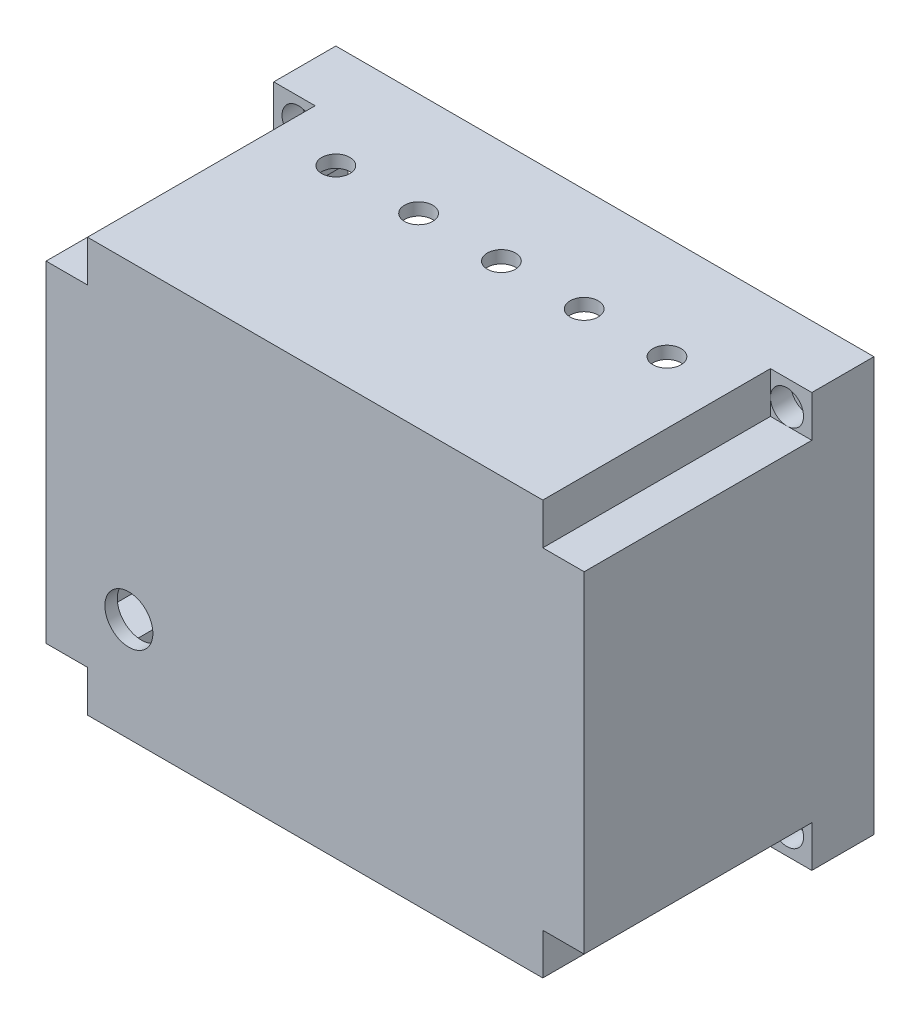
SolidWorks part; units mm, degrees
ref_plane "Front Plane" through (0, 0, 0) normal (0, 0, 1) x (1, 0, 0)
ref_plane "Top Plane" through (0, 0, 0) normal (0, 1, 0) x (1, 0, 0)
ref_plane "Right Plane" through (0, 0, 0) normal (1, 0, 0) x (0, 0, -1)
sketch "Sketch2" plane through (0, 0, 0) normal (0, 1, 0) x (1, 0, 0)
  line L1 (0, 0) -> (130, 0)
  line L2 (0, 0) -> (0, 70)
  line L3 (0, 70) -> (130, 70)
  line L4 (130, 0) -> (130, 70)
  dimension "D1" = 130
  dimension "D2" = 70
extrude "Boss-Extrude1" add sketch "Sketch2" along normal blind 100
sketch "Sketch3" plane through (0, 0, -70) normal (0, 0, -1) x (-1, 0, 0)
  line L0 (-130, 100) -> (0, 100) construction
  line L1 (-117, 87) -> (-13, 87)
  line L2 (-117, 87) -> (-117, 13)
  line L3 (-117, 13) -> (-13, 13)
  line L4 (-13, 87) -> (-13, 13)
  line L5 (-117, 87) -> (-13, 13) construction
  line L6 (-117, 13) -> (-13, 87) construction
  line L7 (-130, 100) -> (-130, 0) construction
  line L8 (-130, 0) -> (0, 0) construction
  line L9 (0, 100) -> (0, 0) construction
  point P0 (-65, 50)
  dimension "D1" = 13
  dimension "D2" = 13
  dimension "D3" = 13
  dimension "D4" = 13
extrude "Cut-Extrude1" cut sketch "Sketch3" against normal blind 67
sketch "Sketch4" plane through (0, 0, 0) normal (0, 0, 1) x (1, 0, 0)
  line L1 (0, 100) -> (10, 100)
  line L2 (0, 100) -> (0, 90)
  line L3 (0, 90) -> (10, 90)
  line L4 (10, 100) -> (10, 90)
  line L5 (130, 100) -> (120, 100)
  line L6 (130, 100) -> (130, 90)
  line L7 (130, 90) -> (120, 90)
  line L8 (120, 100) -> (120, 90)
  line L9 (0, 0) -> (10, 0)
  line L10 (0, 0) -> (0, 10)
  line L11 (0, 10) -> (10, 10)
  line L12 (10, 0) -> (10, 10)
  line L13 (130, 0) -> (120, 0)
  line L14 (130, 0) -> (130, 10)
  line L15 (130, 10) -> (120, 10)
  line L16 (120, 0) -> (120, 10)
  dimension "D1" = 10
  dimension "D2" = 10
  dimension "D3" = 10
  dimension "D4" = 10
  dimension "D5" = 10
  dimension "D6" = 10
  dimension "D7" = 10
  dimension "D8" = 10
extrude "Cut-Extrude2" cut sketch "Sketch4" against normal blind 55
sketch "Sketch5" plane through (0, 0, -70) normal (0, 0, -1) x (-1, 0, 0)
  line L0 (-130, 100) -> (0, 100) construction
  line L1 (-117, 87) -> (-13, 87)
  line L2 (-117, 87) -> (-117, 97)
  line L3 (-117, 97) -> (-13, 97)
  line L4 (-13, 87) -> (-13, 97)
  line L9 (-13, 13) -> (-117, 13)
  line L10 (-13, 13) -> (-13, 3)
  line L11 (-13, 3) -> (-117, 3)
  line L12 (-117, 13) -> (-117, 3)
  line L18 (-130, 0) -> (0, 0) construction
  dimension "D1" = 3
  dimension "D3" = 3
extrude "Cut-Extrude3" cut sketch "Sketch5" against normal blind 67
sketch "Sketch6" plane through (0, 0, -70) normal (0, 0, -1) x (-1, 0, 0)
  line L0 (-117, 97) -> (-117, 3) construction
  line L1 (-117, 87) -> (-127, 87)
  line L2 (-117, 87) -> (-117, 13)
  line L3 (-117, 13) -> (-127, 13)
  line L4 (-127, 87) -> (-127, 13)
  line L5 (-13, 3) -> (-13, 97) construction
  line L6 (-13, 87) -> (-3, 87)
  line L7 (-13, 87) -> (-13, 13)
  line L8 (-13, 13) -> (-3, 13)
  line L9 (-3, 87) -> (-3, 13)
  line L10 (-130, 100) -> (-130, 0) construction
  line L11 (-130, 100) -> (0, 100) construction
  line L12 (-130, 0) -> (0, 0) construction
  line L13 (0, 100) -> (0, 0) construction
  dimension "D1" = 3
  dimension "D2" = 13
  dimension "D3" = 13
  dimension "D4" = 13
  dimension "D5" = 3
  dimension "D6" = 13
extrude "Cut-Extrude4" cut sketch "Sketch6" against normal blind 67
sketch "Sketch9" plane through (0, 0, -70) normal (0, 0, -1) x (-1, 0, 0)
  line L0 (-130, 100) -> (0, 100) construction
  line L1 (-130, 100) -> (-130, 0) construction
  line L2 (0, 100) -> (0, 0) construction
  line L3 (-130, 0) -> (0, 0) construction
  circle A0 centre (-124, 94) radius 1.75
  circle A1 centre (-124, 6) radius 1.75
  circle A2 centre (-6, 94) radius 1.75
  circle A3 centre (-6, 6) radius 1.75
  point P4 (-107.3713, 88.8655)
  point P7 (-7.8416, 92)
  point P8 (-123.9805, 6.1022)
  point P11 (-7.8416, 6.1022)
  point P12 (-122.8257, 93.5015)
  dimension "D1" = 3.5
  dimension "D4" = 3.5
  dimension "D7" = 3.5
  dimension "D10" = 3.5
  dimension "D2" = 6
  dimension "D3" = 6
  dimension "D5" = 6
  dimension "D6" = 6
  dimension "D8" = 6
  dimension "D9" = 6
  dimension "D11" = 6
  dimension "D12" = 6
extrude "Cut-Extrude5" cut sketch "Sketch9" against normal blind 67
sketch "Sketch10" plane through (0, 0, -55) normal (0, 0, 1) x (1, 0, 0)
  line L0 (130, 100) -> (120, 100) construction
  line L1 (130, 90) -> (130, 100) construction
  circle A0 centre (124, 94) radius 4
  dimension "D3" = 8
  dimension "D1" = 6
  dimension "D2" = 6
extrude "Cut-Extrude6" cut sketch "Sketch10" against normal blind 5
sketch "Sketch12" plane through (0, 0, -55) normal (0, 0, 1) x (1, 0, 0)
  line L0 (130, 0) -> (130, 10) construction
  line L1 (120, 0) -> (130, 0) construction
  circle A0 centre (124, 6) radius 4
  dimension "D3" = 8
  dimension "D1" = 6
  dimension "D2" = 6
extrude "Cut-Extrude7" cut sketch "Sketch12" against normal blind 5
sketch "Sketch13" plane through (0, 0, -55) normal (0, 0, 1) x (1, 0, 0)
  line L0 (0, 0) -> (10, 0) construction
  line L1 (0, 10) -> (0, 0) construction
  circle A0 centre (6, 6) radius 4
  dimension "D3" = 8
  dimension "D1" = 6
  dimension "D2" = 6
extrude "Cut-Extrude8" cut sketch "Sketch13" against normal blind 5
sketch "Sketch14" plane through (0, 0, -55) normal (0, 0, 1) x (1, 0, 0)
  line L0 (0, 100) -> (0, 90) construction
  line L1 (10, 100) -> (0, 100) construction
  circle A0 centre (6, 94) radius 4
  dimension "D3" = 8
  dimension "D1" = 6
  dimension "D2" = 6
extrude "Cut-Extrude9" cut sketch "Sketch14" against normal blind 5
sketch "Sketch15" plane through (0, 0, -70) normal (0, 0, -1) x (-1, 0, 0)
  line L1 (-117, 87) -> (-120, 87)
  line L2 (-117, 87) -> (-117, 90)
  line L3 (-117, 90) -> (-120, 90)
  line L4 (-120, 87) -> (-120, 90)
  line L5 (-117, 13) -> (-120, 13)
  line L6 (-117, 13) -> (-117, 10)
  line L7 (-117, 10) -> (-120, 10)
  line L8 (-120, 13) -> (-120, 10)
  line L9 (-13, 13) -> (-10, 13)
  line L10 (-13, 13) -> (-13, 10)
  line L11 (-13, 10) -> (-10, 10)
  line L12 (-10, 13) -> (-10, 10)
  line L13 (-13, 87) -> (-10, 87)
  line L14 (-13, 87) -> (-13, 90)
  line L15 (-13, 90) -> (-10, 90)
  line L16 (-10, 87) -> (-10, 90)
  dimension "D1" = 3
  dimension "D2" = 3
  dimension "D3" = 3
  dimension "D4" = 3
  dimension "D5" = 3
  dimension "D6" = 3
  dimension "D7" = 3
  dimension "D8" = 3
extrude "Boss-Extrude2" add sketch "Sketch15" along normal blind 5
sketch "Sketch16" plane through (0, 3, 0) normal (0, 1, 0) x (1, 0, 0)
  line L3 (117, 70) -> (41, 70)
  line L4 (117, 70) -> (117, 67)
  line L5 (117, 67) -> (41, 67)
  line L6 (41, 70) -> (41, 67)
  dimension "D1" = 3
  dimension "D2" = 76
extrude "Boss-Extrude3" add sketch "Sketch16" along normal blind 15
sketch "Sketch17" plane through (0, 0, -3) normal (0, 0, -1) x (-1, 0, 0)
  line L0 (-117, 18) -> (-41, 18) construction
  line L1 (-101, 18) -> (-98, 18)
  line L2 (-101, 18) -> (-101, 48)
  line L3 (-101, 48) -> (-98, 48)
  line L4 (-98, 18) -> (-98, 48)
  line L5 (-117, 18) -> (-117, 13) construction
  line L6 (-38, 18) -> (-35, 18)
  line L7 (-38, 18) -> (-38, 48)
  line L8 (-38, 48) -> (-35, 48)
  line L9 (-35, 18) -> (-35, 48)
  dimension "D1" = 30
  dimension "D2" = 30
  dimension "D3" = 3
  dimension "D4" = 3
  dimension "D5" = 16
  dimension "D6" = 60
extrude "Boss-Extrude4" add sketch "Sketch17" along normal blind 15
sketch "Sketch18" plane through (0, 0, -3) normal (0, 0, -1) x (-1, 0, 0)
  line L0 (-130, 0) -> (0, 0) construction
  line L1 (0, 100) -> (0, 0) construction
  circle A0 centre (-20, 25) radius 5.8
  dimension "D1" = 11.6
  dimension "D2" = 25
  dimension "D3" = 20
extrude "Cut-Extrude10" cut sketch "Sketch18" against normal blind 15
sketch "Sketch19" plane through (0, 100, 0) normal (0, 1, 0) x (1, 0, 0)
  line L2 (0, 70) -> (0, 45) construction
  line L3 (0, 55) -> (0, 0) construction
  line L4 (0, 45) -> (130, 45) construction
  line L5 (130, 55) -> (130, 0) construction
  line L6 (10, 55) -> (10, 0) construction
  circle A0 centre (25, 45) radius 3.4
  circle A1 centre (45, 45) radius 3.4
  circle A2 centre (65, 45) radius 3.4
  circle A3 centre (85, 45) radius 3.4
  circle A4 centre (105, 45) radius 3.4
  dimension "D7" = 6.8
  dimension "D8" = 6.8
  dimension "D9" = 6.8
  dimension "D10" = 6.8
  dimension "D11" = 6.8
  dimension "D1" = 25
  dimension "D2" = 15
  dimension "D3" = 95
  dimension "D4" = 75
  dimension "D5" = 55
  dimension "D6" = 35
extrude "Cut-Extrude11" cut sketch "Sketch19" against normal blind 15
